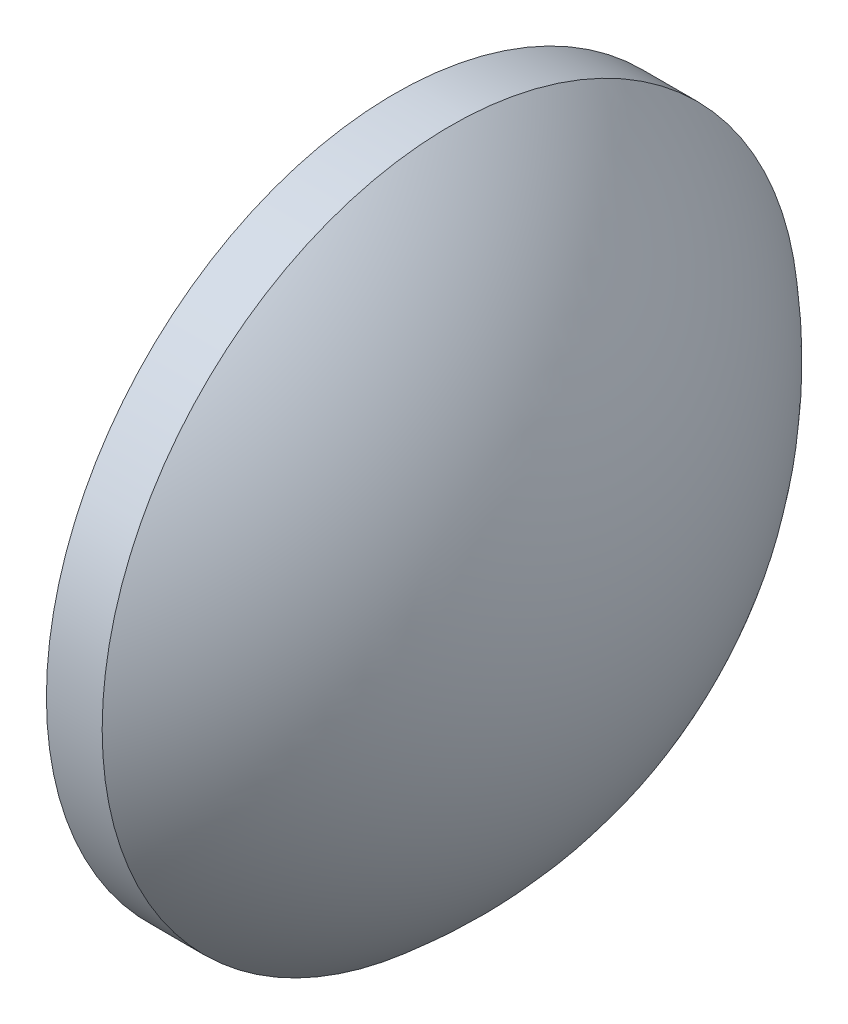
SolidWorks part; units mm, degrees
ref_plane "前视基准面" through (0, 0, 0) normal (0, 0, 1) x (1, 0, 0)
ref_plane "上视基准面" through (0, 0, 0) normal (0, 1, 0) x (1, 0, 0)
ref_plane "右视基准面" through (0, 0, 0) normal (1, 0, 0) x (0, 0, -1)
sketch "草图1" plane through (0, 0, 0) normal (0, 0, 1) x (1, 0, 0)
  line L0 (407.2792, -5.2292) -> (423.3362, -5.2292) construction
  line L1 (409.3083, -5.2292) -> (409.3083, 7.2708)
  line L2 (417.1683, -5.2292) -> (409.3083, -5.2292)
  line L5 (409.3083, 7.2708) -> (411.3083, 7.2708)
  arc A0 (417.1683, -5.2292) -> (411.3083, 7.2708) centre (400.9064, -5.2292) ccw
revolve "旋转1" add sketch "草图1" angle 360 about L0
